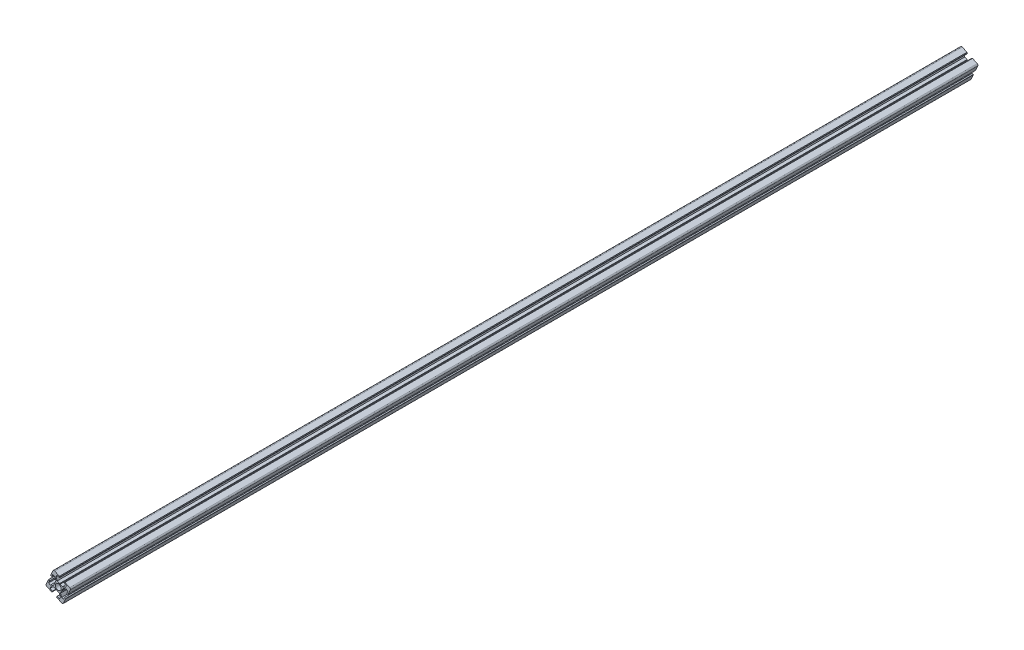
SolidWorks part; units mm, degrees
material "1060 Alloy"
ref_plane "Front" through (0, 0, 0) normal (0, 0, 1) x (1, 0, 0)
ref_plane "Top" through (0, 0, 0) normal (0, 1, 0) x (1, 0, 0)
ref_plane "Right" through (0, 0, 0) normal (1, 0, 0) x (0, 0, -1)
sketch "Sketch1" plane through (0, 0, 0) normal (0, 0, 1) x (1, 0, 0)
  line L0 (-8.2163, 18.0691) -> (-11.8426, 10.1609)
  line L1 (-11.6949, 9.7631) -> (-10.1496, 9.0546)
  line L2 (-10.1496, 9.0546) -> (-8.3782, 12.9178)
  line L3 (-8.3782, 12.9178) -> (-5.346, 11.5274)
  line L4 (-5.346, 11.5274) -> (-3.5425, 6.6693)
  line L5 (-3.5425, 6.6693) -> (-5.2374, 2.9732)
  line L6 (-5.2374, 2.9732) -> (-5.1813, 2.3758)
  line L7 (-5.1813, 2.3758) -> (-5.6705, 2.0286)
  line L8 (-5.6705, 2.0286) -> (-7.3654, -1.6675)
  line L9 (-7.3654, -1.6675) -> (-12.2234, -3.471)
  line L10 (-12.2234, -3.471) -> (-15.2556, -2.0806)
  line L11 (-15.2556, -2.0806) -> (-13.4841, 1.7826)
  line L12 (-13.4841, 1.7826) -> (-15.0294, 2.4912)
  line L13 (-15.4272, 2.3436) -> (-19.0535, -5.5647)
  line L14 (-18.0691, -8.2163) -> (-10.1609, -11.8426)
  line L15 (-9.7631, -11.6949) -> (-9.0546, -10.1496)
  line L16 (-9.0546, -10.1496) -> (-12.9178, -8.3782)
  line L17 (-12.9178, -8.3782) -> (-11.5274, -5.346)
  line L18 (-11.5274, -5.346) -> (-6.6693, -3.5425)
  line L19 (-6.6693, -3.5425) -> (-2.9732, -5.2374)
  line L20 (-2.9732, -5.2374) -> (-2.3758, -5.1813)
  line L21 (1.9074, 15.6272) -> (-5.5647, 19.0535)
  line L22 (2.3758, 5.1813) -> (2.9732, 5.2374)
  line L23 (2.9732, 5.2374) -> (6.6693, 3.5425)
  line L24 (12.9178, 8.3782) -> (8.9517, 10.1968)
  line L26 (10.597, 11.6426) -> (18.0691, 8.2163)
  line L27 (11.5274, 5.346) -> (12.9178, 8.3782)
  line L28 (6.6693, 3.5425) -> (11.5274, 5.346)
  line L29 (-2.0286, -5.6705) -> (-2.3758, -5.1813)
  line L30 (1.6675, -7.3654) -> (-2.0286, -5.6705)
  line L31 (3.471, -12.2234) -> (1.6675, -7.3654)
  line L32 (2.0806, -15.2556) -> (3.471, -12.2234)
  line L33 (-1.7826, -13.4841) -> (2.0806, -15.2556)
  line L34 (2.3758, 5.1813) -> (2.0286, 5.6705)
  line L35 (2.0286, 5.6705) -> (-1.6675, 7.3654)
  line L36 (-1.6675, 7.3654) -> (-3.471, 12.2234)
  line L37 (-3.471, 12.2234) -> (-2.0806, 15.2556)
  line L38 (-2.0806, 15.2556) -> (1.8855, 13.437)
  line L40 (2.3758, 5.1813) -> (-2.3758, -5.1813) construction
  line L41 (-2.4912, -15.0294) -> (-1.7826, -13.4841)
  line L42 (5.5647, -19.0535) -> (-2.3436, -15.4272)
  line L43 (11.8426, -10.1609) -> (8.2163, -18.0691)
  line L44 (10.1496, -9.0546) -> (11.6949, -9.7631)
  line L45 (8.3782, -12.9178) -> (10.1496, -9.0546)
  line L46 (5.346, -11.5274) -> (8.3782, -12.9178)
  line L47 (3.5425, -6.6693) -> (5.346, -11.5274)
  line L48 (5.2374, -2.9732) -> (3.5425, -6.6693)
  line L49 (5.1813, -2.3758) -> (5.2374, -2.9732)
  line L50 (5.6705, -2.0286) -> (5.1813, -2.3758)
  line L51 (7.3654, 1.6675) -> (5.6705, -2.0286)
  line L52 (12.2234, 3.471) -> (7.3654, 1.6675)
  line L53 (15.2556, 2.0806) -> (12.2234, 3.471)
  line L54 (13.4841, -1.7826) -> (15.2556, 2.0806)
  line L55 (15.0294, -2.4912) -> (13.4841, -1.7826)
  line L56 (19.0535, 5.5647) -> (15.4272, -2.3436)
  line L57 (1.8855, 13.437) -> (2.3469, 14.4432)
  line L58 (2.3469, 14.4432) -> (1.9074, 15.6272)
  line L59 (8.9517, 10.1968) -> (9.4131, 11.2031)
  line L60 (9.4131, 11.2031) -> (10.597, 11.6426)
  arc A0 (-5.5647, 19.0535) -> (-8.2163, 18.0691) centre (-6.3983, 17.2355) ccw
  arc A1 (-11.8426, 10.1609) -> (-11.6949, 9.7631) centre (-11.5699, 10.0358) ccw
  arc A2 (-15.0294, 2.4912) -> (-15.4272, 2.3436) centre (-15.1545, 2.2185) ccw
  arc A3 (-19.0535, -5.5647) -> (-18.0691, -8.2163) centre (-17.2355, -6.3983) ccw
  arc A4 (-10.1609, -11.8426) -> (-9.7631, -11.6949) centre (-10.0358, -11.5699) ccw
  arc A6 (-2.3436, -15.4272) -> (-2.4912, -15.0294) centre (-2.2185, -15.1545) cw
  arc A7 (8.2163, -18.0691) -> (5.5647, -19.0535) centre (6.3983, -17.2355) cw
  arc A8 (11.6949, -9.7631) -> (11.8426, -10.1609) centre (11.5699, -10.0358) cw
  arc A10 (15.4272, -2.3436) -> (15.0294, -2.4912) centre (15.1545, -2.2185) cw
  arc A11 (18.0691, 8.2163) -> (19.0535, 5.5647) centre (17.2355, 6.3983) cw
  dimension "D1" = 45
  dimension "D2" = 30
extrude "Boss-Extrude1" add sketch "Sketch1" along normal blind 2000
scale "Scale1" scale about centroid uniform scaling yes scale factor 3
sketch "Sketch2" plane through (0, 0, -2000) normal (0, 0, -1) x (-1, 0, 0)
  circle A0 centre (0, 0) radius 115.0478
extrude "Cut-Extrude1" cut sketch "Sketch2" against normal blind 1600
sketch "Sketch3" plane through (0, 0, 4000) normal (0, 0, 1) x (1, 0, 0)
  circle A0 centre (0, 0) radius 13.75
  dimension "D1" = 27.5
extrude "Cut-Extrude2" cut sketch "Sketch3" against normal through all
scale "Scale2" bodies to scale 104 scale about centroid uniform scaling yes scale factor 0.466667
sketch "Sketch6" plane through (0, 0, 773.3333) normal (0, 0, -1) x (-1, 0, 0)
  line L58 (7.7891, 26.678) -> (-2.6718, 21.8811)
  line L59 (-2.6718, 21.8811) -> (-3.2872, 20.2236)
  line L60 (-3.2872, 20.2236) -> (-2.6412, 18.8149)
  line L61 (-2.6412, 18.8149) -> (2.9114, 21.361)
  line L62 (2.9114, 21.361) -> (4.858, 17.1159)
  line L63 (4.858, 17.1159) -> (2.3331, 10.3146)
  line L64 (2.3331, 10.3146) -> (-2.8414, 7.9419)
  line L65 (-2.8414, 7.9419) -> (-3.3276, 7.2569)
  line L66 (-3.3276, 7.2569) -> (-4.1639, 7.3354)
  line L67 (-4.1639, 7.3354) -> (-9.3385, 4.9626)
  line L68 (-9.3385, 4.9626) -> (-16.1397, 7.4875)
  line L69 (-16.1397, 7.4875) -> (-18.0863, 11.7325)
  line L70 (-18.0863, 11.7325) -> (-12.5338, 14.2786)
  line L71 (-12.5338, 14.2786) -> (-13.1797, 15.6874)
  line L72 (-13.1797, 15.6874) -> (-14.8373, 16.3027)
  line L73 (-14.8373, 16.3027) -> (-25.2982, 11.5059)
  line L74 (-26.6763, 7.7936) -> (-21.5995, -3.2779)
  line L75 (-21.0426, -3.4846) -> (-18.8792, -2.4926)
  line L76 (-18.8792, -2.4926) -> (-21.3593, 2.9159)
  line L77 (-21.3593, 2.9159) -> (-17.1142, 4.8625)
  line L78 (-17.1142, 4.8625) -> (-10.3129, 2.3377)
  line L79 (-10.3129, 2.3377) -> (-7.9402, -2.8369)
  line L80 (-7.9402, -2.8369) -> (-7.2552, -3.3231)
  line L81 (-7.2552, -3.3231) -> (-7.3337, -4.1594)
  line L82 (-7.3337, -4.1594) -> (-4.961, -9.334)
  line L83 (-4.961, -9.334) -> (-7.4858, -16.1352)
  line L84 (-7.4858, -16.1352) -> (-11.7309, -18.0818)
  line L85 (-11.7309, -18.0818) -> (-14.2109, -12.6733)
  line L86 (-14.2109, -12.6733) -> (-16.3743, -13.6653)
  line L87 (-16.581, -14.2221) -> (-11.5042, -25.2936)
  line L88 (-7.7919, -26.6717) -> (3.2796, -21.5949)
  line L89 (3.4863, -21.0381) -> (2.4943, -18.8747)
  line L90 (2.4943, -18.8747) -> (-2.9142, -21.3547)
  line L91 (-2.9142, -21.3547) -> (-4.8608, -17.1097)
  line L92 (-4.8608, -17.1097) -> (-2.336, -10.3084)
  line L93 (-2.336, -10.3084) -> (2.8386, -7.9356)
  line L94 (2.8386, -7.9356) -> (3.3248, -7.2506)
  line L95 (3.3248, -7.2506) -> (4.1611, -7.3292)
  line L96 (4.1611, -7.3292) -> (9.3356, -4.9564)
  line L97 (9.3356, -4.9564) -> (16.1369, -7.4812)
  line L98 (16.1369, -7.4812) -> (18.0835, -11.7263)
  line L99 (18.0835, -11.7263) -> (12.675, -14.2064)
  line L100 (12.675, -14.2064) -> (13.667, -16.3698)
  line L101 (14.2238, -16.5765) -> (25.2953, -11.4997)
  line L102 (26.6734, -7.7874) -> (21.5966, 3.2841)
  line L103 (21.0398, 3.4908) -> (18.8764, 2.4988)
  line L104 (18.8764, 2.4988) -> (21.3564, -2.9097)
  line L105 (21.3564, -2.9097) -> (17.1113, -4.8563)
  line L106 (17.1113, -4.8563) -> (10.3101, -2.3315)
  line L107 (10.3101, -2.3315) -> (7.9373, 2.8431)
  line L108 (7.9373, 2.8431) -> (7.2523, 3.3293)
  line L109 (7.2523, 3.3293) -> (7.3309, 4.1656)
  line L110 (7.3309, 4.1656) -> (4.9581, 9.3402)
  line L111 (4.9581, 9.3402) -> (7.4829, 16.1414)
  line L112 (7.4829, 16.1414) -> (11.728, 18.088)
  line L113 (11.728, 18.088) -> (14.208, 12.6795)
  line L114 (14.208, 12.6795) -> (16.3714, 13.6715)
  line L115 (16.5782, 14.2284) -> (11.5014, 25.2999)
  line L116 (7.7891, 26.678) -> (-2.6718, 21.8811)
  line L117 (-2.6718, 21.8811) -> (-3.2872, 20.2236)
  line L118 (-3.2872, 20.2236) -> (-2.6412, 18.8149)
  line L119 (-2.6412, 18.8149) -> (2.9114, 21.361)
  line L120 (2.9114, 21.361) -> (4.858, 17.1159)
  line L121 (4.858, 17.1159) -> (2.3331, 10.3146)
  line L122 (2.3331, 10.3146) -> (-2.8414, 7.9419)
  line L123 (-2.8414, 7.9419) -> (-3.3276, 7.2569)
  line L124 (-3.3276, 7.2569) -> (-4.1639, 7.3354)
  line L125 (-4.1639, 7.3354) -> (-9.3385, 4.9626)
  line L126 (-9.3385, 4.9626) -> (-16.1397, 7.4875)
  line L127 (-16.1397, 7.4875) -> (-18.0863, 11.7325)
  line L128 (-18.0863, 11.7325) -> (-12.5338, 14.2786)
  line L129 (-12.5338, 14.2786) -> (-13.1797, 15.6874)
  line L130 (-13.1797, 15.6874) -> (-14.8373, 16.3027)
  line L131 (-14.8373, 16.3027) -> (-25.2982, 11.5059)
  line L132 (-26.6763, 7.7936) -> (-21.5995, -3.2779)
  line L133 (-21.0426, -3.4846) -> (-18.8792, -2.4926)
  line L134 (-18.8792, -2.4926) -> (-21.3593, 2.9159)
  line L135 (-21.3593, 2.9159) -> (-17.1142, 4.8625)
  line L136 (-17.1142, 4.8625) -> (-10.3129, 2.3377)
  line L137 (-10.3129, 2.3377) -> (-7.9402, -2.8369)
  line L138 (-7.9402, -2.8369) -> (-7.2552, -3.3231)
  line L139 (-7.2552, -3.3231) -> (-7.3337, -4.1594)
  line L140 (-7.3337, -4.1594) -> (-4.961, -9.334)
  line L141 (-4.961, -9.334) -> (-7.4858, -16.1352)
  line L142 (-7.4858, -16.1352) -> (-11.7309, -18.0818)
  line L143 (-11.7309, -18.0818) -> (-14.2109, -12.6733)
  line L144 (-14.2109, -12.6733) -> (-16.3743, -13.6653)
  line L145 (-16.581, -14.2221) -> (-11.5042, -25.2936)
  line L146 (-7.7919, -26.6717) -> (3.2796, -21.5949)
  line L147 (3.4863, -21.0381) -> (2.4943, -18.8747)
  line L148 (2.4943, -18.8747) -> (-2.9142, -21.3547)
  line L149 (-2.9142, -21.3547) -> (-4.8608, -17.1097)
  line L150 (-4.8608, -17.1097) -> (-2.336, -10.3084)
  line L151 (-2.336, -10.3084) -> (2.8386, -7.9356)
  line L152 (2.8386, -7.9356) -> (3.3248, -7.2506)
  line L153 (3.3248, -7.2506) -> (4.1611, -7.3292)
  line L154 (4.1611, -7.3292) -> (9.3356, -4.9564)
  line L155 (9.3356, -4.9564) -> (16.1369, -7.4812)
  line L156 (16.1369, -7.4812) -> (18.0835, -11.7263)
  line L157 (18.0835, -11.7263) -> (12.675, -14.2064)
  line L158 (12.675, -14.2064) -> (13.667, -16.3698)
  line L159 (14.2238, -16.5765) -> (25.2953, -11.4997)
  line L160 (26.6734, -7.7874) -> (21.5966, 3.2841)
  line L161 (21.0398, 3.4908) -> (18.8764, 2.4988)
  line L162 (18.8764, 2.4988) -> (21.3564, -2.9097)
  line L163 (21.3564, -2.9097) -> (17.1113, -4.8563)
  line L164 (17.1113, -4.8563) -> (10.3101, -2.3315)
  line L165 (10.3101, -2.3315) -> (7.9373, 2.8431)
  line L166 (7.9373, 2.8431) -> (7.2523, 3.3293)
  line L167 (7.2523, 3.3293) -> (7.3309, 4.1656)
  line L168 (7.3309, 4.1656) -> (4.9581, 9.3402)
  line L169 (4.9581, 9.3402) -> (7.4829, 16.1414)
  line L170 (7.4829, 16.1414) -> (11.728, 18.088)
  line L171 (11.728, 18.088) -> (14.208, 12.6795)
  line L172 (14.208, 12.6795) -> (16.3714, 13.6715)
  line L173 (16.5782, 14.2284) -> (11.5014, 25.2999)
  arc A10 (11.5014, 25.2999) -> (7.7891, 26.678) centre (8.9562, 24.1328) ccw
  arc A11 (-25.2982, 11.5059) -> (-26.6763, 7.7936) centre (-24.1311, 8.9607) ccw
  arc A12 (-21.5995, -3.2779) -> (-21.0426, -3.4846) centre (-21.2177, -3.1028) ccw
  arc A13 (-16.3743, -13.6653) -> (-16.581, -14.2221) centre (-16.1992, -14.0471) ccw
  arc A14 (-11.5042, -25.2936) -> (-7.7919, -26.6717) centre (-8.959, -24.1266) ccw
  arc A15 (3.2796, -21.5949) -> (3.4863, -21.0381) centre (3.1045, -21.2132) ccw
  arc A16 (13.667, -16.3698) -> (14.2238, -16.5765) centre (14.0488, -16.1947) ccw
  arc A17 (25.2953, -11.4997) -> (26.6734, -7.7874) centre (24.1282, -8.9545) ccw
  arc A18 (21.5966, 3.2841) -> (21.0398, 3.4908) centre (21.2148, 3.109) ccw
  arc A19 (16.3714, 13.6715) -> (16.5782, 14.2284) centre (16.1964, 14.0533) ccw
  arc A20 (11.5014, 25.2999) -> (7.7891, 26.678) centre (8.9562, 24.1328) ccw
  arc A21 (-25.2982, 11.5059) -> (-26.6763, 7.7936) centre (-24.1311, 8.9607) ccw
  arc A22 (-21.5995, -3.2779) -> (-21.0426, -3.4846) centre (-21.2177, -3.1028) ccw
  arc A23 (-16.3743, -13.6653) -> (-16.581, -14.2221) centre (-16.1992, -14.0471) ccw
  arc A24 (-11.5042, -25.2936) -> (-7.7919, -26.6717) centre (-8.959, -24.1266) ccw
  arc A25 (3.2796, -21.5949) -> (3.4863, -21.0381) centre (3.1045, -21.2132) ccw
  arc A26 (13.667, -16.3698) -> (14.2238, -16.5765) centre (14.0488, -16.1947) ccw
  arc A27 (25.2953, -11.4997) -> (26.6734, -7.7874) centre (24.1282, -8.9545) ccw
  arc A28 (21.5966, 3.2841) -> (21.0398, 3.4908) centre (21.2148, 3.109) ccw
  arc A29 (16.3714, 13.6715) -> (16.5782, 14.2284) centre (16.1964, 14.0533) ccw
  dimension "D1" = 0
extrude "Cut-Extrude3" cut sketch "Sketch6" against normal blind 53.3
